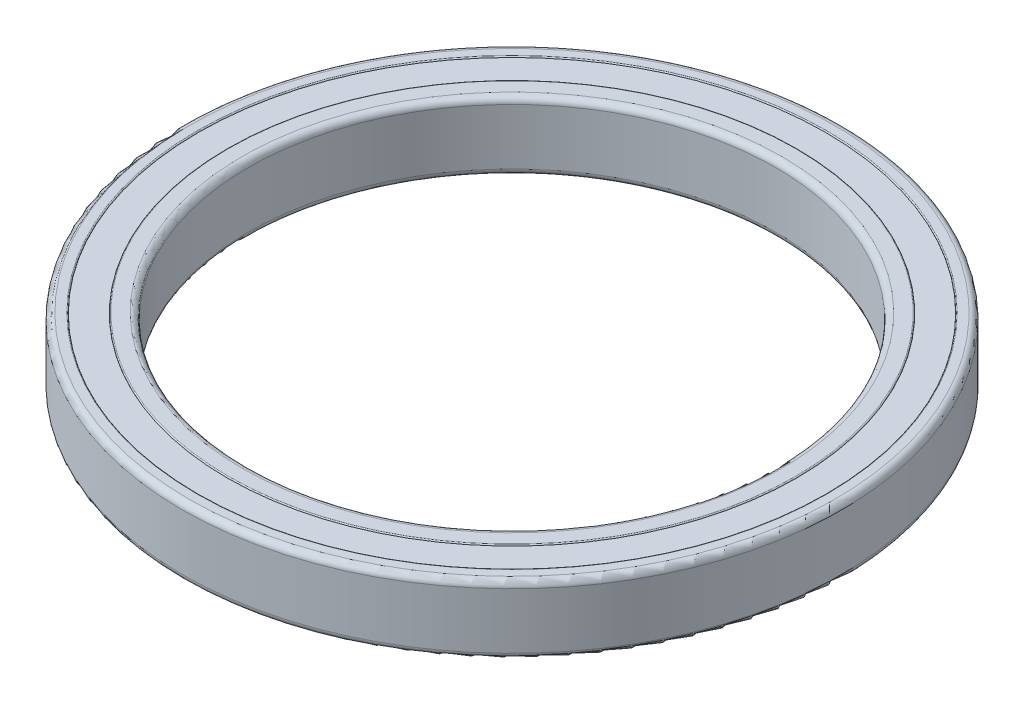
SolidWorks part; units mm, degrees
ref_plane "Ebene vorne" through (0, 0, 0) normal (0, 0, 1) x (1, 0, 0)
ref_plane "Ebene oben" through (0, 0, 0) normal (0, 1, 0) x (1, 0, 0)
ref_plane "Ebene rechts" through (0, 0, 0) normal (1, 0, 0) x (0, 0, -1)
sketch "Skizze1" plane through (0, 0, 0) normal (0, 1, 0) x (1, 0, 0)
  circle A0 centre (0, 0) radius 62.5
  circle A1 centre (0, 0) radius 59.5
  dimension "D1" = 125
  dimension "D2" = 119
extrude "Außenring" add sketch "Skizze1" along normal mid plane 13
sketch "Skizze2" plane through (0, 0, 0) normal (0, 1, 0) x (1, 0, 0)
  circle A0 centre (0, 0) radius 50
  circle A1 centre (0, 0) radius 54
  dimension "D1" = 100
  dimension "D2" = 108
extrude "Innenring" add sketch "Skizze2" along normal mid plane 13 separate body
fillet "Verrundung1" radius 1.2 2 edges at (0, -6.5, 62.5) (0, 6.5, 62.5)
fillet "Verrundung2" radius 1.2 2 edges at (0, -6.5, 50) (0, 6.5, 50)
fillet "Verrundung3" radius 0.2 2 edges at (0, -6.5, 54) (0, 6.5, 54)
fillet "Verrundung4" radius 0.2 2 edges at (0, 6.5, 59.5) (0, -6.5, 59.5)
sketch "Skizze3" plane through (0, 0, 0) normal (0, 1, 0) x (1, 0, 0)
  circle A0 centre (0, 0) radius 54
  circle A1 centre (0, 0) radius 54 construction
  circle A2 centre (0, 0) radius 59.5
  circle A3 centre (0, 0) radius 59.5 construction
extrude "Dichtung" add sketch "Skizze3" along normal mid plane 12.6 separate body
